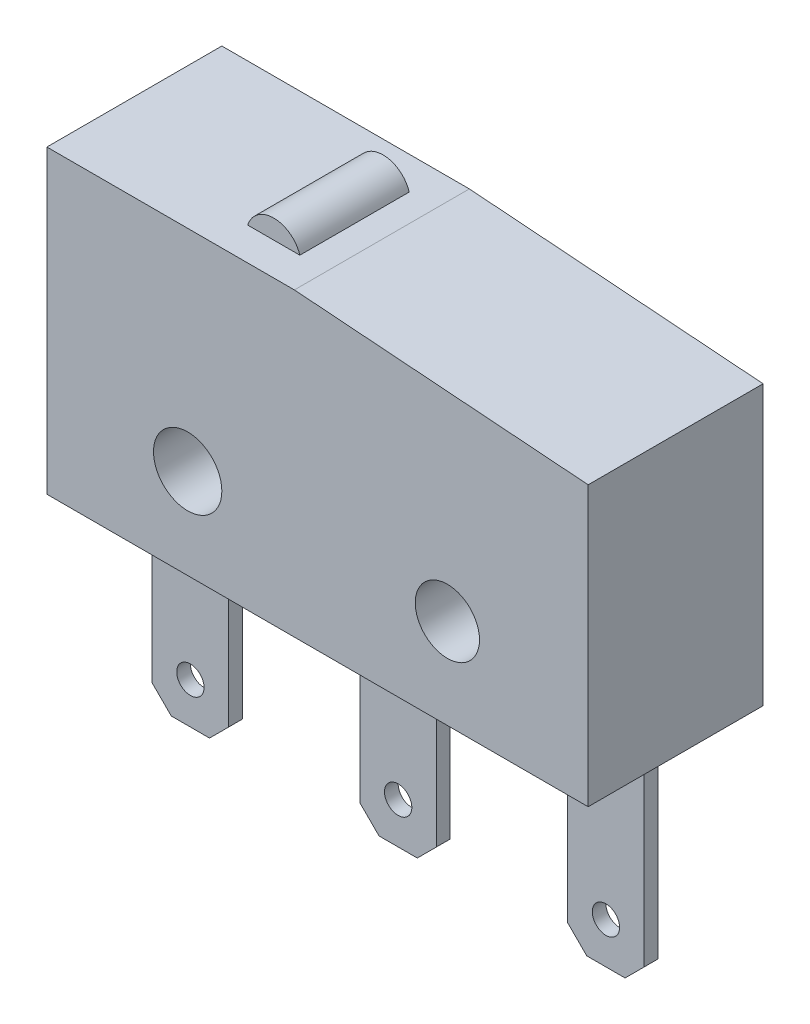
SolidWorks part; units mm, degrees
ref_plane "Front Plane" through (0, 0, 0) normal (0, 0, 1) x (1, 0, 0)
ref_plane "Top Plane" through (0, 0, 0) normal (0, 1, 0) x (1, 0, 0)
ref_plane "Right Plane" through (0, 0, 0) normal (1, 0, 0) x (0, 0, -1)
sketch "Sketch1" plane through (0, 0, 0) normal (0, 0, 1) x (1, 0, 0)
  line L0 (-5.15, -3.3) -> (14.65, -3.3)
  line L1 (14.65, -3.3) -> (14.65, 6.9)
  line L2 (14.65, 6.9) -> (3.9039, 7.7)
  line L3 (3.9039, 7.7) -> (2.9039, 7.7)
  line L4 (-5.15, 7.7) -> (-5.15, -3.3)
  line L7 (0.9961, 7.7) -> (-5.15, 7.7)
  circle A0 centre (0, 0) radius 1.25
  circle A1 centre (9.5, 0) radius 1.175
  arc A2 (2.9039, 7.7) -> (0.9961, 7.7) centre (1.95, 7.4) ccw
  dimension "D1" = 2.5
  dimension "D2" = 2.35
  dimension "D10" = 8.4
  dimension "D9" = 1
  dimension "D3" = 9.5
  dimension "D4" = 5.15
  dimension "D5" = 6.9
  dimension "D6" = 7.7
  dimension "D7" = 19.8
  dimension "D8" = 3.3
  dimension "D11" = 7.55
  dimension "D12" = 1
extrude "Boss-Extrude1" add sketch "Sketch1" along normal mid plane 6.4
sketch "Sketch2" plane through (0, 0, 0) normal (0, 0, 1) x (1, 0, 0)
  line L0 (-5.15, -3.3) -> (14.65, -3.3) construction
  line L1 (-4.25, -3.3) -> (-1.45, -3.3)
  line L2 (-4.25, -3.3) -> (-4.25, -10.3)
  line L3 (-3.55, -11) -> (-2.15, -11)
  line L4 (-1.45, -3.3) -> (-1.45, -10.3)
  line L5 (12.35, -9.5) -> (12.35, -11) construction
  line L6 (3.35, -3.3) -> (6.15, -3.3)
  line L7 (3.35, -3.3) -> (3.35, -10.3)
  line L8 (4.05, -11) -> (5.45, -11)
  line L9 (6.15, -3.3) -> (6.15, -10.3)
  line L10 (10.95, -3.3) -> (13.75, -3.3)
  line L11 (10.95, -3.3) -> (10.95, -10.3)
  line L12 (11.65, -11) -> (13.05, -11)
  line L13 (13.75, -3.3) -> (13.75, -10.3)
  line L14 (4.75, -9.5) -> (4.75, -11) construction
  line L15 (-2.85, -9.5) -> (-2.85, -11) construction
  line L16 (10.95, -10.3) -> (11.65, -11)
  line L17 (13.05, -11) -> (13.75, -10.3)
  line L18 (5.45, -11) -> (6.15, -10.3)
  line L19 (3.35, -10.3) -> (4.05, -11)
  line L20 (-2.15, -11) -> (-1.45, -10.3)
  line L21 (-4.25, -10.3) -> (-3.55, -11)
  line L22 (-5.15, -3.3) -> (-4.25, -3.3) construction
  line L23 (14.65, -3.3) -> (13.75, -3.3) construction
  circle A0 centre (0, 0) radius 1.25 construction
  circle A1 centre (-2.85, -9.5) radius 0.5
  circle A2 centre (4.75, -9.5) radius 0.5
  circle A3 centre (12.35, -9.5) radius 0.5
  point P1 (-1.45, -11)
  point P2 (-4.25, -11)
  point P7 (6.15, -11)
  point P8 (3.35, -11)
  point P11 (13.75, -11)
  point P12 (10.95, -11)
  dimension "D3" = 1
  dimension "D1" = 2.8
  dimension "D2" = 11
  dimension "D4" = 7.6
  dimension "D5" = 7.6
  dimension "D6" = 1.5
extrude "Boss-Extrude2" add sketch "Sketch2" along normal mid plane 0.5
sketch "Sketch3" plane through (0, 7.7, 0) normal (0, 1, 0) x (1, 0, 0)
  line L0 (3.9039, -3.2) -> (3.9039, 3.2) construction
  line L1 (0.9961, 3.2) -> (3.9039, 3.2)
  line L2 (0.9961, 3.2) -> (0.9961, 2)
  line L3 (0.9961, 2) -> (3.9039, 2)
  line L4 (3.9039, 3.2) -> (3.9039, 2)
  line L6 (0.9961, -3.2) -> (3.9039, -3.2)
  line L7 (0.9961, -3.2) -> (0.9961, -2)
  line L8 (0.9961, -2) -> (3.9039, -2)
  line L9 (3.9039, -3.2) -> (3.9039, -2)
  dimension "D1" = 1.2
extrude "Cut-Extrude1" cut sketch "Sketch3" along normal through all
